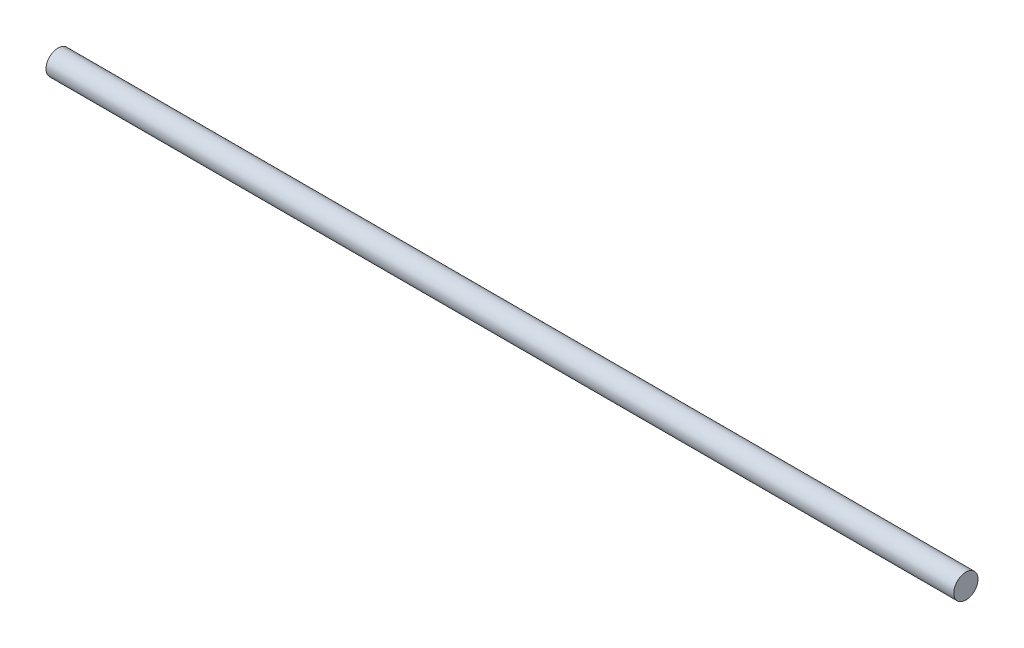
SolidWorks part; units mm, degrees
material "Chrome Stainless Steel"
ref_plane "Front Plane" through (0, 0, 0) normal (0, 0, 1) x (1, 0, 0)
ref_plane "Top Plane" through (0, 0, 0) normal (0, 1, 0) x (1, 0, 0)
ref_plane "Right Plane" through (0, 0, 0) normal (1, 0, 0) x (0, 0, -1)
sketch "Sketch1" plane through (0, 0, 0) normal (1, 0, 0) x (0, 0, -1)
  circle A0 centre (0, 0) radius 4
extrude "Boss-Extrude1" add sketch "Sketch1" along normal blind 300
